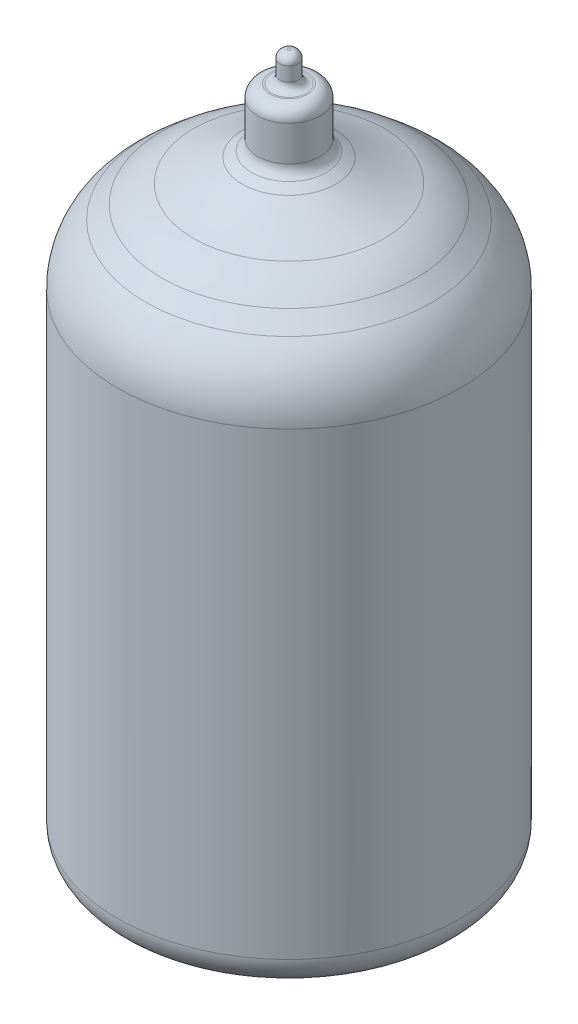
SolidWorks part; units mm, degrees
material "Glass"
ref_plane "Front Plane" through (0, 0, 0) normal (0, 0, 1) x (1, 0, 0)
ref_plane "Top Plane" through (0, 0, 0) normal (0, 1, 0) x (1, 0, 0)
ref_plane "Right Plane" through (0, 0, 0) normal (1, 0, 0) x (0, 0, -1)
ref_plane "Plane1" through (0, 0, 0) normal (1, 0, 0) x (0, 0, -1)
sketch "Sketch1" plane through (0, 0, 0) normal (1, 0, 0) x (0, 0, -1)
  line L0 (11, 35) -> (11, 3.2064)
  line L1 (3, 39.9723) -> (0, 39.9723)
  line L2 (11, 3.2064) -> (0, 3.2064)
  line L3 (0, 39.9723) -> (0, 3.2064)
  line L4 (0, 41.8106) -> (0, 1.3681) construction
  line L5 (11, 35) -> (7.1684, 38.1619)
  arc A0 (3, 39.9723) -> (7.1684, 38.1619) centre (13, 57.2928) ccw
revolve "Revolve1" add sketch "Sketch1" angle 360 about L4
fillet "Fillet1" radius 5 1 edges at (0, 35, 11)
fillet "Fillet2" radius 7 1 edges at (0, 38.1619, 7.1684)
shell "Shell1" thickness 0.6
ref_plane "Plane2" through (0, 0, 0) normal (1, 0, 0) x (0, -1, 0)
sketch "Sketch2" plane through (0, 0, 0) normal (1, 0, 0) x (0, -1, 0)
  line L0 (-39.9723, 3) -> (-40.3187, 2.4)
  line L1 (-41.0115, 2) -> (-43.2723, 2)
  line L2 (-44.0723, 1.2) -> (-44.0723, 1.1)
  line L3 (-44.5723, 0.6) -> (-45.4723, 0.6)
  line L4 (-45.9723, 0.1) -> (-45.9723, 0)
  line L5 (-39.9723, 3) -> (-39.9723, 0)
  line L6 (-39.9723, 0) -> (-45.9723, 0)
  line L7 (-46.2723, 0) -> (-39.6723, 0) construction
  arc A0 (-43.2723, 2) -> (-44.0723, 1.2) centre (-43.2723, 1.2) ccw
  arc A1 (-41.0115, 2) -> (-40.3187, 2.4) centre (-41.0115, 2.8) ccw
  arc A2 (-44.5723, 0.6) -> (-44.0723, 1.1) centre (-44.5723, 1.1) ccw
  arc A3 (-45.4723, 0.6) -> (-45.9723, 0.1) centre (-45.4723, 0.1) ccw
revolve "Revolve2" add sketch "Sketch2" angle 360 about L7
ref_plane "Plane3" through (0, 0, 0) normal (0, 0, 1) x (1, 0, 0)
sketch "Sketch3" plane through (0, 0, 0) normal (0, 0, 1) x (1, 0, 0)
  line L0 (0, 0) -> (-5.7855, 0)
  line L1 (-6.4695, 0.1206) -> (-9.684, 1.2906)
  line L2 (-11, 3.2064) -> (-11, 3.17)
  line L3 (-11, 3.2064) -> (-10.4, 3.2064)
  line L4 (-10.4, 3.2064) -> (-10.4, 3.12)
  line L5 (-10, 2.72) -> (0, 2.72)
  line L6 (0, 2.72) -> (0, 0)
  line L7 (0, 3.3667) -> (0, -0.1603) construction
  arc A0 (-10.4, 3.12) -> (-10, 2.72) centre (-10, 3.12) ccw
  arc A1 (-11, 3.17) -> (-9.684, 1.2906) centre (-9, 3.17) ccw
  arc A2 (-6.4695, 0.1206) -> (-5.7855, 0) centre (-5.7855, 2) ccw
revolve "Revolve3" add sketch "Sketch3" angle 360 about L7
ref_plane "Plane4" through (0, 0, 0) normal (-0.5878, 0, 0.809) x (0.809, 0, 0.5878)
sketch "Sketch4" plane through (0, 0, 0) normal (-0.5878, 0, 0.809) x (0.809, 0, 0.5878)
  line L0 (7.65, 2) -> (6.9455, 4.6294)
  line L1 (6.4625, 5) -> (5.95, 5)
  line L2 (5.95, 2) -> (7.65, 2)
  line L3 (5.95, 5) -> (5.95, 2)
  line L4 (5.95, 1.85) -> (5.95, 5.15) construction
  arc A0 (6.9455, 4.6294) -> (6.4625, 5) centre (6.4625, 4.5) ccw
revolve "Revolve4" add sketch "Sketch4" angle 360 about L4
ref_plane "Plane5" through (0, 0, 0) normal (-0.9511, 0, 0.309) x (0.309, 0, 0.9511)
sketch "Sketch5" plane through (0, 0, 0) normal (-0.9511, 0, 0.309) x (0.309, 0, 0.9511)
  line L0 (7.65, 2) -> (6.9455, 4.6294)
  line L1 (6.4625, 5) -> (5.95, 5)
  line L2 (5.95, 2) -> (7.65, 2)
  line L3 (5.95, 5) -> (5.95, 2)
  line L4 (5.95, 1.85) -> (5.95, 5.15) construction
  arc A0 (6.9455, 4.6294) -> (6.4625, 5) centre (6.4625, 4.5) ccw
revolve "Revolve5" add sketch "Sketch5" angle 360 about L4
ref_plane "Plane6" through (0, 0, 0) normal (-0.9511, 0, -0.309) x (-0.309, 0, 0.9511)
sketch "Sketch6" plane through (0, 0, 0) normal (-0.9511, 0, -0.309) x (-0.309, 0, 0.9511)
  line L0 (7.65, 2) -> (6.9455, 4.6294)
  line L1 (6.4625, 5) -> (5.95, 5)
  line L2 (5.95, 2) -> (7.65, 2)
  line L3 (5.95, 5) -> (5.95, 2)
  line L4 (5.95, 1.85) -> (5.95, 5.15) construction
  arc A0 (6.9455, 4.6294) -> (6.4625, 5) centre (6.4625, 4.5) ccw
revolve "Revolve6" add sketch "Sketch6" angle 360 about L4
ref_plane "Plane7" through (0, 0, 0) normal (-0.5878, 0, -0.809) x (-0.809, 0, 0.5878)
sketch "Sketch7" plane through (0, 0, 0) normal (-0.5878, 0, -0.809) x (-0.809, 0, 0.5878)
  line L0 (7.65, 2) -> (6.9455, 4.6294)
  line L1 (6.4625, 5) -> (5.95, 5)
  line L2 (5.95, 2) -> (7.65, 2)
  line L3 (5.95, 5) -> (5.95, 2)
  line L4 (5.95, 1.85) -> (5.95, 5.15) construction
  arc A0 (6.9455, 4.6294) -> (6.4625, 5) centre (6.4625, 4.5) ccw
revolve "Revolve7" add sketch "Sketch7" angle 360 about L4
ref_plane "Plane8" through (0, 0, 0) normal (0, 0, -1) x (-1, 0, 0)
sketch "Sketch8" plane through (0, 0, 0) normal (0, 0, -1) x (-1, 0, 0)
  line L0 (7.65, 2) -> (6.9455, 4.6294)
  line L1 (6.4625, 5) -> (5.95, 5)
  line L2 (5.95, 2) -> (7.65, 2)
  line L3 (5.95, 5) -> (5.95, 2)
  line L4 (5.95, 1.85) -> (5.95, 5.15) construction
  arc A0 (6.9455, 4.6294) -> (6.4625, 5) centre (6.4625, 4.5) ccw
revolve "Revolve8" add sketch "Sketch8" angle 360 about L4
ref_plane "Plane9" through (0, 0, 0) normal (0.5878, 0, -0.809) x (-0.809, 0, -0.5878)
sketch "Sketch9" plane through (0, 0, 0) normal (0.5878, 0, -0.809) x (-0.809, 0, -0.5878)
  line L0 (7.65, 2) -> (6.9455, 4.6294)
  line L1 (6.4625, 5) -> (5.95, 5)
  line L2 (5.95, 2) -> (7.65, 2)
  line L3 (5.95, 5) -> (5.95, 2)
  line L4 (5.95, 1.85) -> (5.95, 5.15) construction
  arc A0 (6.9455, 4.6294) -> (6.4625, 5) centre (6.4625, 4.5) ccw
revolve "Revolve9" add sketch "Sketch9" angle 360 about L4
ref_plane "Plane10" through (0, 0, 0) normal (0.9511, 0, -0.309) x (-0.309, 0, -0.9511)
sketch "Sketch10" plane through (0, 0, 0) normal (0.9511, 0, -0.309) x (-0.309, 0, -0.9511)
  line L0 (7.65, 2) -> (6.9455, 4.6294)
  line L1 (6.4625, 5) -> (5.95, 5)
  line L2 (5.95, 2) -> (7.65, 2)
  line L3 (5.95, 5) -> (5.95, 2)
  line L4 (5.95, 1.85) -> (5.95, 5.15) construction
  arc A0 (6.9455, 4.6294) -> (6.4625, 5) centre (6.4625, 4.5) ccw
revolve "Revolve10" add sketch "Sketch10" angle 360 about L4
ref_plane "Plane11" through (0, 0, 0) normal (0.9511, 0, 0.309) x (0.309, 0, -0.9511)
sketch "Sketch11" plane through (0, 0, 0) normal (0.9511, 0, 0.309) x (0.309, 0, -0.9511)
  line L0 (7.65, 2) -> (6.9455, 4.6294)
  line L1 (6.4625, 5) -> (5.95, 5)
  line L2 (5.95, 2) -> (7.65, 2)
  line L3 (5.95, 5) -> (5.95, 2)
  line L4 (5.95, 1.85) -> (5.95, 5.15) construction
  arc A0 (6.9455, 4.6294) -> (6.4625, 5) centre (6.4625, 4.5) ccw
revolve "Revolve11" add sketch "Sketch11" angle 360 about L4
ref_plane "Plane12" through (0, 0, 0) normal (0.5878, 0, 0.809) x (0.809, 0, -0.5878)
sketch "Sketch12" plane through (0, 0, 0) normal (0.5878, 0, 0.809) x (0.809, 0, -0.5878)
  line L0 (7.65, 2) -> (6.9455, 4.6294)
  line L1 (6.4625, 5) -> (5.95, 5)
  line L2 (5.95, 2) -> (7.65, 2)
  line L3 (5.95, 5) -> (5.95, 2)
  line L4 (5.95, 1.85) -> (5.95, 5.15) construction
  arc A0 (6.9455, 4.6294) -> (6.4625, 5) centre (6.4625, 4.5) ccw
revolve "Revolve12" add sketch "Sketch12" angle 360 about L4
